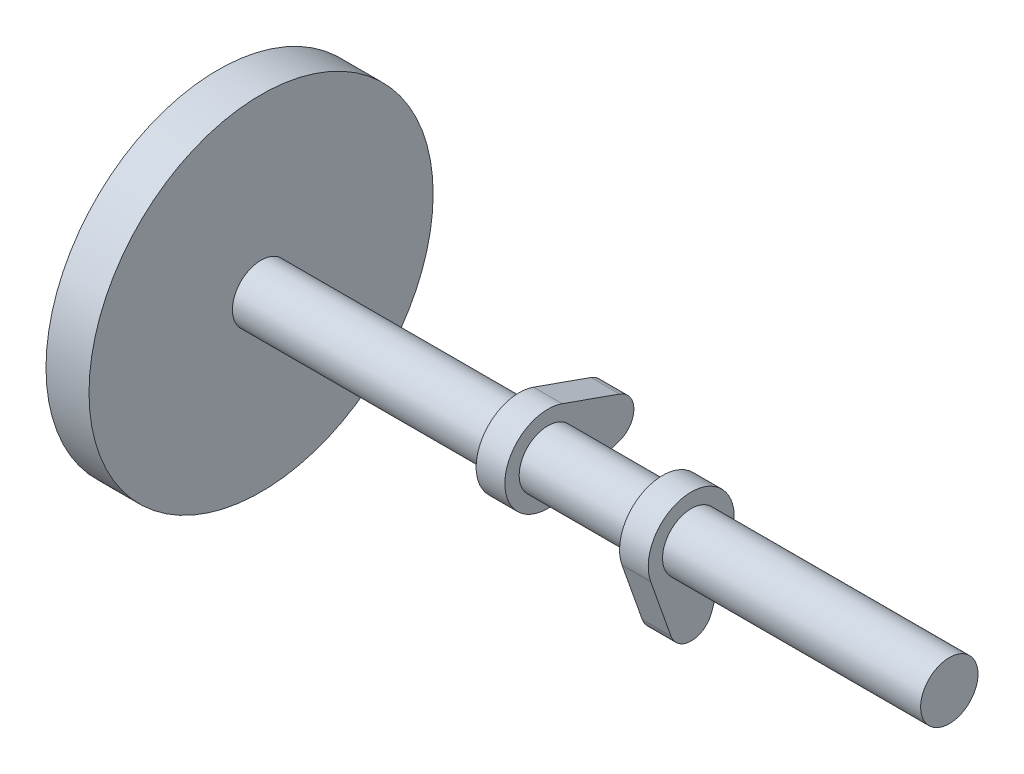
SolidWorks part; units mm, degrees
ref_plane "Front" through (0, 0, 0) normal (0, 0, 1) x (1, 0, 0)
ref_plane "Top" through (0, 0, 0) normal (0, 1, 0) x (1, 0, 0)
ref_plane "Right" through (0, 0, 0) normal (1, 0, 0) x (0, 0, -1)
sketch "Sketch1" plane through (0, 0, 0) normal (1, 0, 0) x (0, 0, -1)
  circle A0 centre (0, 0) radius 10
  dimension "D1" = 20
extrude "Boss-Extrude1" add sketch "Sketch1" along normal mid plane 240
ref_plane "Plane1" through (25, 0, 0) normal (1, 0, 0) x (0, 0, -1)
sketch "Sketch2" plane through (25, 0, 0) normal (1, 0, 0) x (0, 0, -1)
  line L0 (0, 0) -> (0, -22.5)
  line L1 (-14.1421, -5) -> (-7.0711, -25)
  line L2 (14.1421, -5) -> (7.0711, -25)
  circle A0 centre (0, 0) radius 10
  circle A1 centre (0, 0) radius 10
  circle A2 centre (0, 0) radius 15
  circle A3 centre (0, -22.5) radius 7.5
  dimension "D2" = 15
  dimension "D1" = 5
sketch "Sketch3" plane through (25, 0, 0) normal (1, 0, 0) x (0, 0, -1)
  line L0 (14.1421, -5) -> (7.0711, -25) construction
  line L1 (-14.1421, -5) -> (-7.0711, -25) construction
  line L2 (0, 0) -> (0, -22.5) construction
  line L3 (14.1421, -5) -> (7.0711, -25)
  line L4 (-14.1421, -5) -> (-7.0711, -25)
  line L5 (0, 0) -> (0, -10)
  circle A1 centre (0, -22.5) radius 7.5
  arc A2 (-7.0711, -25) -> (7.0711, -25) centre (0, -22.5) ccw
  circle A3 centre (0, 0) radius 15
  arc A4 (14.1421, -5) -> (-14.1421, -5) centre (0, 0) ccw
  circle A5 centre (0, 0) radius 10
  circle A6 centre (0, 0) radius 10
  dimension "D1" = 0
  dimension "D2" = 0
  dimension "D3" = 0
extrude "Boss-Extrude2" add sketch "Sketch3" along normal mid plane 10 separate body contours L3 A4 L4 A2 A6
mirror "Mirror1" about plane through (0, 0, 0) normal (1, 0, 0) of bodies 102
move or copy body "Body-Move/Copy1" bodies to move or copy 103 copy no rotation origin (0, 0, 0) rotation axis (1, 0, 0) rotation angle 90
combine bodies "Combine1" operation type add bodies to combine 101 102 104
ref_plane "Plane2" through (-25, 0, 0) normal (1, 0, 0) x (0, 0, -1)
sketch "Sketch4" plane through (-25, 0, 0) normal (1, 0, 0) x (0, 0, -1)
  line L0 (25, -7.0711) -> (5, -14.1421)
  line L1 (25, -7.0711) -> (5, -14.1421)
  line L2 (25, 7.0711) -> (5, 14.1421)
  line L3 (25, 7.0711) -> (5, 14.1421)
  arc A0 (25, -7.0711) -> (25, 7.0711) centre (22.5, 0) ccw
  arc A1 (25, -7.0711) -> (25, 7.0711) centre (22.5, 0) ccw
  arc A2 (5, 14.1421) -> (5, -14.1421) centre (0, 0) ccw
  arc A3 (5, 14.1421) -> (5, -14.1421) centre (0, 0) ccw
sketch "Sketch5" plane through (-120, 0, 0) normal (-1, 0, 0) x (0, 0, 1)
  circle A0 centre (0, 0) radius 60
  dimension "D1" = 120
extrude "Boss-Extrude3" add sketch "Sketch5" along normal blind 15 separate body
